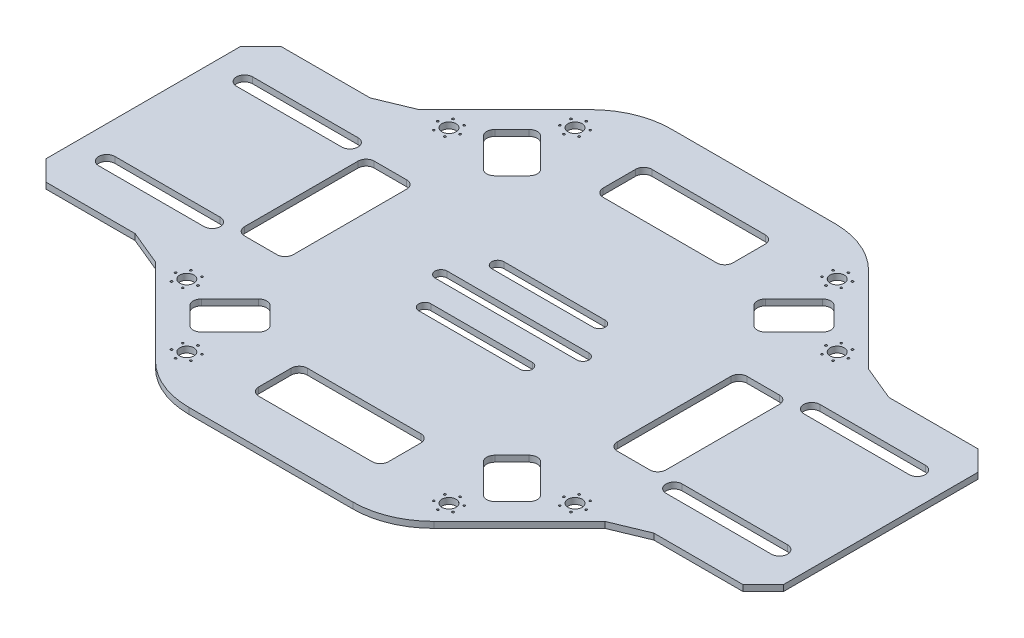
SolidWorks part; units mm, degrees
ref_plane "Front Plane" through (0, 0, 0) normal (0, 0, 1) x (1, 0, 0)
ref_plane "Top Plane" through (0, 0, 0) normal (0, 1, 0) x (1, 0, 0)
ref_plane "Right Plane" through (0, 0, 0) normal (1, 0, 0) x (0, 0, -1)
sketch "Sketch1" plane through (0, 0, 0) normal (0, 1, 0) x (1, 0, 0)
  line L0 (0, 0) -> (0, 340.9146) construction
  line L1 (0, 0) -> (552.6048, 0) construction
  line L2 (28.5, 59.5) -> (-28.5, 59.5)
  line L4 (59, 29) -> (91, 29)
  line L5 (91, 29) -> (91, -29)
  line L6 (59, -29) -> (91, -29)
  line L8 (28.5, -59.5) -> (-28.5, -59.5)
  line L10 (-59, -29) -> (-91, -29)
  line L11 (-91, 29) -> (-91, -29)
  line L12 (-59, 29) -> (-91, 29)
  line L14 (28.5, 59.5) -> (59, 29)
  line L15 (59, -29) -> (28.5, -59.5)
  line L16 (-59, 29) -> (-28.5, 59.5)
  line L17 (-59, -29) -> (-28.5, -59.5)
  point P3 (-91, 0)
  point P10 (91, 0)
  point P14 (0, -59.5)
  point P19 (0, 59.5)
  dimension "D1" = 182
  dimension "D2" = 119
  dimension "D3" = 32
  dimension "D4" = 45
  dimension "D5" = 58
extrude "Boss-Extrude1" add sketch "Sketch1" along normal blind 1.5
chamfer "Chamfer1" distance 5 angle 45 4 edges at (-91, 0.75, -29) (-91, 0.75, 29) (91, 0.75, 29) (91, 0.75, -29)
fillet "Fillet1" radius 20 4 edges at (28.5, 0.75, 59.5) (-28.5, 0.75, 59.5) (-28.5, 0.75, -59.5) (28.5, 0.75, -59.5)
chamfer "Chamfer2" distance 5 4 edges at (59, 0.75, 29) (-59, 0.75, 29) (-59, 0.75, -29) (59, 0.75, -29)
sketch "Sketch3" plane through (0, 1.5, 0) normal (0, 1, 0) x (1, 0, 0)
  line L0 (0, 0) -> (-70.5095, 70.5095) construction
  line L1 (0, 0) -> (72.4144, 72.4144) construction
  line L2 (0, 0) -> (-91, 0) construction
  line L3 (-91, 24) -> (-91, -24) construction
  circle A0 centre (-32.3501, 47.9065) radius 1.75
  circle A1 centre (-47.9065, 32.3501) radius 1.75
  circle A3 centre (32.3501, 47.9065) radius 1.75
  circle A4 centre (47.9065, 32.3501) radius 1.75
  circle A5 centre (47.9065, -32.3501) radius 1.75
  circle A6 centre (32.3501, -47.9065) radius 1.75
  circle A7 centre (-32.3501, -47.9065) radius 1.75
  circle A8 centre (-47.9065, -32.3501) radius 1.75
  point P11 (32.3501, -47.9065)
  point P27 (0, 0)
  dimension "D2" = 3.5
  dimension "D3" = 22
  dimension "D1" = 45
  dimension "D4" = 56.75
  dimension "D5" = 4
extrude "Cut-Extrude1" cut sketch "Sketch3" against normal through all
sketch "Sketch4" plane through (0, 1.5, 0) normal (0, 1, 0) x (1, 0, 0)
  line L0 (57, 17) -> (83, 17) construction
  line L1 (57, 19) -> (83, 19)
  line L2 (57, 15) -> (83, 15)
  line L3 (-17.5, 0) -> (17.5, 0) construction
  line L4 (-17.5, 1.5) -> (17.5, 1.5)
  line L5 (-17.5, -1.5) -> (17.5, -1.5)
  line L6 (-12.5, 9) -> (12.5, 9) construction
  line L7 (-12.5, 10.5) -> (12.5, 10.5)
  line L8 (-12.5, 7.5) -> (12.5, 7.5)
  line L9 (0, 0) -> (109.8094, 0) construction
  line L10 (-16, 48.5) -> (16, 48.5)
  line L11 (-16, 48.5) -> (-16, 36.5)
  line L12 (-16, 36.5) -> (16, 36.5)
  line L13 (16, 48.5) -> (16, 36.5)
  line L14 (40, 16) -> (52, 16)
  line L15 (40, 16) -> (40, -16)
  line L16 (40, -16) -> (52, -16)
  line L17 (52, 16) -> (52, -16)
  line L18 (0, 0) -> (0, 75.8422) construction
  line L19 (91, -24) -> (91, 24) construction
  line L20 (86, 29) -> (64, 29) construction
  line L21 (57, -17) -> (83, -17) construction
  line L22 (57, -19) -> (83, -19)
  line L23 (57, -15) -> (83, -15)
  line L24 (-12.5, -9) -> (12.5, -9) construction
  line L25 (-12.5, -10.5) -> (12.5, -10.5)
  line L26 (-12.5, -7.5) -> (12.5, -7.5)
  line L27 (20.2157, 59.5) -> (-20.2157, 59.5) construction
  line L28 (-40, -16) -> (-52, -16)
  line L29 (-40, 16) -> (-40, -16)
  line L30 (-40, 16) -> (-52, 16)
  line L31 (-52, 16) -> (-52, -16)
  line L32 (-57, -17) -> (-83, -17) construction
  line L33 (-57, -19) -> (-83, -19)
  line L34 (-57, -15) -> (-83, -15)
  line L35 (-57, 17) -> (-83, 17) construction
  line L36 (-57, 19) -> (-83, 19)
  line L37 (-57, 15) -> (-83, 15)
  line L38 (16, -48.5) -> (16, -36.5)
  line L39 (-16, -48.5) -> (16, -48.5)
  line L40 (-16, -48.5) -> (-16, -36.5)
  line L41 (-16, -36.5) -> (16, -36.5)
  arc A0 (57, 19) -> (57, 15) centre (57, 17) ccw
  arc A1 (83, 15) -> (83, 19) centre (83, 17) ccw
  arc A2 (-17.5, 1.5) -> (-17.5, -1.5) centre (-17.5, 0) ccw
  arc A3 (17.5, -1.5) -> (17.5, 1.5) centre (17.5, 0) ccw
  arc A4 (-12.5, 10.5) -> (-12.5, 7.5) centre (-12.5, 9) ccw
  arc A5 (12.5, 7.5) -> (12.5, 10.5) centre (12.5, 9) ccw
  arc A6 (57, -19) -> (57, -15) centre (57, -17) cw
  arc A7 (83, -15) -> (83, -19) centre (83, -17) cw
  arc A8 (-12.5, -10.5) -> (-12.5, -7.5) centre (-12.5, -9) cw
  arc A9 (12.5, -7.5) -> (12.5, -10.5) centre (12.5, -9) cw
  arc A10 (-57, -19) -> (-57, -15) centre (-57, -17) ccw
  arc A11 (-83, -15) -> (-83, -19) centre (-83, -17) ccw
  arc A12 (-57, 19) -> (-57, 15) centre (-57, 17) cw
  arc A13 (-83, 15) -> (-83, 19) centre (-83, 17) cw
  point P2 (70, 17)
  point P7 (0, 0)
  point P15 (0, 9)
  point P32 (-10.4787, 9)
  point P38 (0, 17)
  point P41 (70, -17)
  point P46 (0, 10.6599)
  point P47 (0, 0)
  point P48 (0, 9)
  point P49 (0, 9)
  point P52 (0, -9)
  point P65 (-70, -17)
  point P72 (-70, 17)
  dimension "D7" = 2
  dimension "D10" = 1.5
  dimension "D12" = 1.5
  dimension "D1" = 12
  dimension "D2" = 32
  dimension "D3" = 12
  dimension "D4" = 32
  dimension "D5" = 39
  dimension "D6" = 26
  dimension "D8" = 8
  dimension "D9" = 10
  dimension "D11" = 35
  dimension "D13" = 25
  dimension "D14" = 6
  dimension "D15" = 11
extrude "Cut-Extrude2" cut sketch "Sketch4" against normal blind 1.5
fillet "Fillet2" radius 2 16 edges at (-40, 0.75, -16) (-40, 0.75, 16) (-52, 0.75, 16) (-52, 0.75, -16) (16, 0.75, 36.5) (16, 0.75, 48.5) (-16, 0.75, 48.5) (-16, 0.75, 36.5) (52, 0.75, 16) (40, 0.75, 16) (40, 0.75, -16) (52, 0.75, -16) (-16, 0.75, -36.5) (16, 0.75, -36.5) (16, 0.75, -48.5) (-16, 0.75, -48.5)
sketch "Sketch5" plane through (0, 1.5, 0) normal (0, 1, 0) x (1, 0, 0)
  line L0 (0, 0) -> (-59.8676, 59.8676) construction
  line L1 (-41.8787, 37.636) -> (-37.636, 41.8787)
  line L2 (-34.8076, 41.8787) -> (-27.7365, 34.8076)
  line L3 (-27.7365, 31.9792) -> (-31.9792, 27.7365)
  line L4 (-34.8076, 27.7365) -> (-41.8787, 34.8076)
  line L5 (-34.3579, 53.6421) -> (-55.4645, 32.5355) construction
  line L6 (31.9792, 27.7365) -> (27.7365, 31.9792)
  line L7 (27.7365, 34.8076) -> (34.8076, 41.8787)
  line L8 (37.636, 41.8787) -> (41.8787, 37.636)
  line L9 (41.8787, 34.8076) -> (34.8076, 27.7365)
  line L10 (27.7365, -31.9792) -> (31.9792, -27.7365)
  line L11 (34.8076, -27.7365) -> (41.8787, -34.8076)
  line L12 (41.8787, -37.636) -> (37.636, -41.8787)
  line L13 (34.8076, -41.8787) -> (27.7365, -34.8076)
  line L14 (-31.9792, -27.7365) -> (-27.7365, -31.9792)
  line L15 (-27.7365, -34.8076) -> (-34.8076, -41.8787)
  line L16 (-37.636, -41.8787) -> (-41.8787, -37.636)
  line L17 (-41.8787, -34.8076) -> (-34.8076, -27.7365)
  arc A0 (-41.8787, 37.636) -> (-41.8787, 34.8076) centre (-40.4645, 36.2218) ccw
  arc A1 (-31.9792, 27.7365) -> (-34.8076, 27.7365) centre (-33.3934, 29.1508) cw
  arc A2 (-27.7365, 34.8076) -> (-27.7365, 31.9792) centre (-29.1508, 33.3934) cw
  arc A3 (-37.636, 41.8787) -> (-34.8076, 41.8787) centre (-36.2218, 40.4645) cw
  arc A4 (34.8076, 27.7365) -> (31.9792, 27.7365) centre (33.3934, 29.1508) cw
  arc A5 (27.7365, 31.9792) -> (27.7365, 34.8076) centre (29.1508, 33.3934) cw
  arc A6 (37.636, 41.8787) -> (34.8076, 41.8787) centre (36.2218, 40.4645) ccw
  arc A7 (41.8787, 37.636) -> (41.8787, 34.8076) centre (40.4645, 36.2218) cw
  arc A8 (27.7365, -34.8076) -> (27.7365, -31.9792) centre (29.1508, -33.3934) cw
  arc A9 (31.9792, -27.7365) -> (34.8076, -27.7365) centre (33.3934, -29.1508) cw
  arc A10 (41.8787, -37.636) -> (41.8787, -34.8076) centre (40.4645, -36.2218) ccw
  arc A11 (37.636, -41.8787) -> (34.8076, -41.8787) centre (36.2218, -40.4645) cw
  arc A12 (-34.8076, -27.7365) -> (-31.9792, -27.7365) centre (-33.3934, -29.1508) cw
  arc A13 (-27.7365, -31.9792) -> (-27.7365, -34.8076) centre (-29.1508, -33.3934) cw
  arc A14 (-37.636, -41.8787) -> (-34.8076, -41.8787) centre (-36.2218, -40.4645) ccw
  arc A15 (-41.8787, -37.636) -> (-41.8787, -34.8076) centre (-40.4645, -36.2218) cw
  point P56 (0, 0)
  dimension "D4" = 2
  dimension "D1" = 6
  dimension "D2" = 10
  dimension "D3" = 14
  dimension "D5" = 4
extrude "Cut-Extrude3" cut sketch "Sketch5" against normal blind 1.5
sketch "Sketch6" plane through (0, 1.5, 0) normal (0, 1, 0) x (1, 0, 0)
  line L0 (-29.8579, 29.8579) -> (-39.7574, 39.7574) construction
  line L1 (-31.9792, 27.7365) -> (-27.7365, 31.9792) construction
  line L2 (-37.636, 41.8787) -> (-41.8787, 37.636) construction
  circle A0 centre (-32.3501, 47.9065) radius 2.75 construction
  circle A1 centre (-32.3501, 50.6565) radius 0.25
  circle A2 centre (-29.9686, 49.2815) radius 0.25
  circle A3 centre (-29.9686, 46.5315) radius 0.25
  circle A4 centre (-32.3501, 45.1565) radius 0.25
  circle A5 centre (-34.7317, 46.5315) radius 0.25
  circle A6 centre (-34.7317, 49.2815) radius 0.25
  circle A7 centre (-49.2815, 34.7317) radius 0.25
  circle A8 centre (-46.5315, 34.7317) radius 0.25
  circle A9 centre (-45.1565, 32.3501) radius 0.25
  circle A10 centre (-46.5315, 29.9686) radius 0.25
  circle A11 centre (-49.2815, 29.9686) radius 0.25
  circle A12 centre (-50.6565, 32.3501) radius 0.25
  circle A13 centre (-50.6565, -32.3501) radius 0.25
  circle A14 centre (-49.2815, -29.9686) radius 0.25
  circle A15 centre (-46.5315, -29.9686) radius 0.25
  circle A16 centre (-45.1565, -32.3501) radius 0.25
  circle A17 centre (-46.5315, -34.7317) radius 0.25
  circle A18 centre (-49.2815, -34.7317) radius 0.25
  circle A19 centre (-34.7317, -46.5315) radius 0.25
  circle A20 centre (-32.3501, -45.1565) radius 0.25
  circle A21 centre (-29.9686, -46.5315) radius 0.25
  circle A22 centre (-29.9686, -49.2815) radius 0.25
  circle A23 centre (-32.3501, -50.6565) radius 0.25
  circle A24 centre (-34.7317, -49.2815) radius 0.25
  circle A25 centre (32.3501, -50.6565) radius 0.25
  circle A26 centre (29.9686, -49.2815) radius 0.25
  circle A27 centre (29.9686, -46.5315) radius 0.25
  circle A28 centre (32.3501, -45.1565) radius 0.25
  circle A29 centre (34.7317, -46.5315) radius 0.25
  circle A30 centre (34.7317, -49.2815) radius 0.25
  circle A31 centre (46.5315, -34.7317) radius 0.25
  circle A32 centre (45.1565, -32.3501) radius 0.25
  circle A33 centre (46.5315, -29.9686) radius 0.25
  circle A34 centre (49.2815, -29.9686) radius 0.25
  circle A35 centre (50.6565, -32.3501) radius 0.25
  circle A36 centre (49.2815, -34.7317) radius 0.25
  circle A37 centre (50.6565, 32.3501) radius 0.25
  circle A38 centre (49.2815, 29.9686) radius 0.25
  circle A39 centre (46.5315, 29.9686) radius 0.25
  circle A40 centre (45.1565, 32.3501) radius 0.25
  circle A41 centre (46.5315, 34.7317) radius 0.25
  circle A42 centre (49.2815, 34.7317) radius 0.25
  circle A43 centre (34.7317, 46.5315) radius 0.25
  circle A44 centre (32.3501, 45.1565) radius 0.25
  circle A45 centre (29.9686, 46.5315) radius 0.25
  circle A46 centre (29.9686, 49.2815) radius 0.25
  circle A47 centre (32.3501, 50.6565) radius 0.25
  circle A48 centre (34.7317, 49.2815) radius 0.25
  point P17 (-32.3501, 47.9065)
  point P109 (0, 0)
  dimension "D1" = 5.5
  dimension "D2" = 0.5
  dimension "D3" = 6
  dimension "D4" = 4
extrude "Cut-Extrude4" cut sketch "Sketch6" against normal blind 1.5
